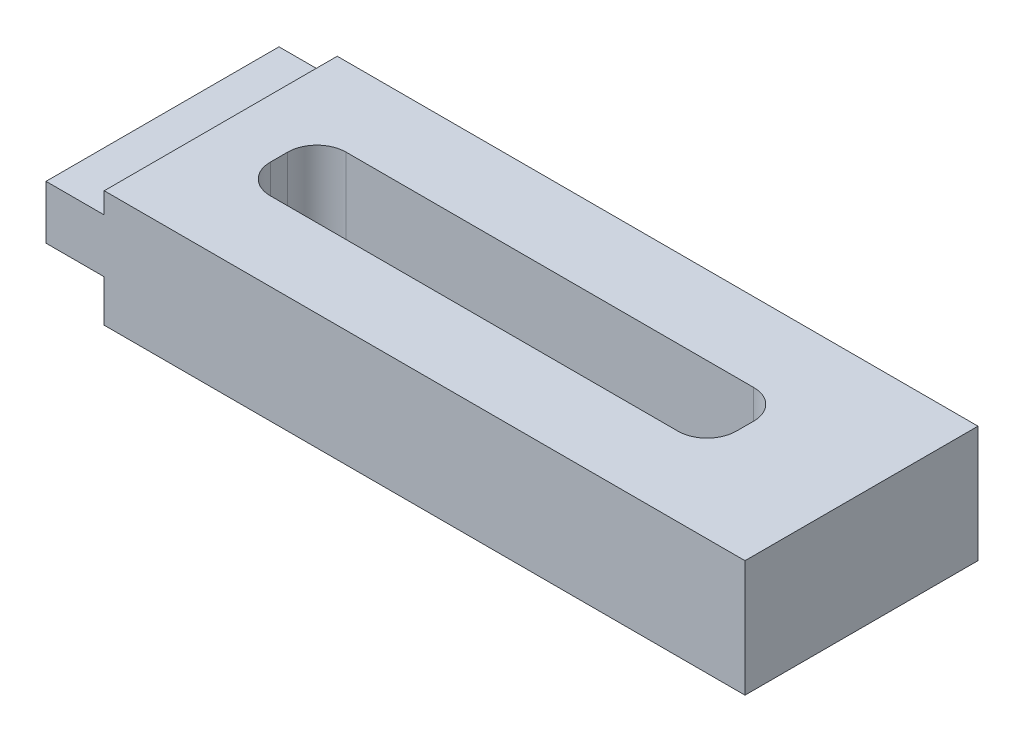
SolidWorks part; units mm, degrees
ref_plane "Front Plane" through (0, 0, 0) normal (0, 0, 1) x (1, 0, 0)
ref_plane "Top Plane" through (0, 0, 0) normal (0, 1, 0) x (1, 0, 0)
ref_plane "Right Plane" through (0, 0, 0) normal (1, 0, 0) x (0, 0, -1)
sketch "Sketch1" plane through (0, 0, 0) normal (0, 1, 0) x (1, 0, 0)
  line L1 (0, 0) -> (76.2, 0)
  line L2 (0, 0) -> (0, 25.4)
  line L3 (0, 25.4) -> (76.2, 25.4)
  line L4 (76.2, 0) -> (76.2, 25.4)
  dimension "D1" = 25.4
  dimension "D2" = 76.2
extrude "Boss-Extrude1" add sketch "Sketch1" along normal blind 12.7
sketch "Sketch3" plane through (0, 12.7, 0) normal (0, 1, 0) x (1, 0, 0)
  line L7 (15.875, 8.5725) -> (60.325, 8.5725)
  line L8 (12.7, 11.7475) -> (12.7, 13.6525)
  line L9 (15.875, 16.8275) -> (60.325, 16.8275)
  line L10 (63.5, 11.7475) -> (63.5, 13.6525)
  arc A0 (60.325, 8.5725) -> (63.5, 11.7475) centre (60.325, 11.7475) ccw
  arc A1 (15.875, 8.5725) -> (12.7, 11.7475) centre (15.875, 11.7475) cw
  arc A2 (15.875, 16.8275) -> (12.7, 13.6525) centre (15.875, 13.6525) ccw
  arc A3 (60.325, 16.8275) -> (63.5, 13.6525) centre (60.325, 13.6525) cw
  point P12 (12.7, 12.7)
  point P13 (63.5, 12.7)
  dimension "D2" = 3.175
  dimension "D1" = 3.175
  dimension "D3" = 3.175
  dimension "D4" = 3.175
extrude "Cut-Extrude1" cut sketch "Sketch3" against normal through all
sketch "Sketch4" plane through (0, 0, 0) normal (0, 0, 1) x (1, 0, 0)
  line L0 (0, 12.7) -> (0, 0) construction
  line L1 (0, 4.572) -> (6.35, 4.572)
  line L2 (0, 4.572) -> (0, 0)
  line L3 (0, 0) -> (6.35, 0)
  line L4 (6.35, 4.572) -> (6.35, 0)
  line L5 (0, 0) -> (76.2, 0) construction
  line L7 (0, 12.7) -> (6.35, 12.7)
  line L8 (0, 12.7) -> (0, 10.414)
  line L9 (0, 10.414) -> (6.35, 10.414)
  line L10 (6.35, 12.7) -> (6.35, 10.414)
  dimension "D1" = 6.35
  dimension "D2" = 4.572
  dimension "D3" = 2.286
extrude "Cut-Extrude2" cut sketch "Sketch4" against normal through all
